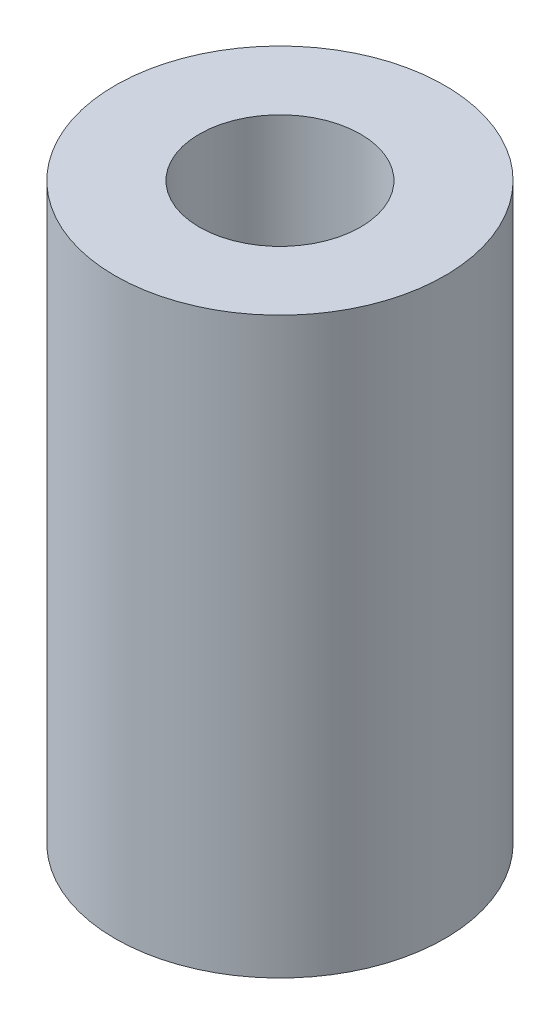
SolidWorks part; units mm, degrees
material "Propellant"
ref_plane "Front Plane" through (0, 0, 0) normal (0, 0, 1) x (1, 0, 0)
ref_plane "Top Plane" through (0, 0, 0) normal (0, 1, 0) x (1, 0, 0)
ref_plane "Right Plane" through (0, 0, 0) normal (1, 0, 0) x (0, 0, -1)
sketch "Sketch1" plane through (0, 0, 0) normal (0, 1, 0) x (1, 0, 0)
  circle A0 centre (0, 0) radius 32.4612
  circle A1 centre (0, 0) radius 15.875
extrude "Boss-Extrude1" add sketch "Sketch1" along normal blind 113.03
